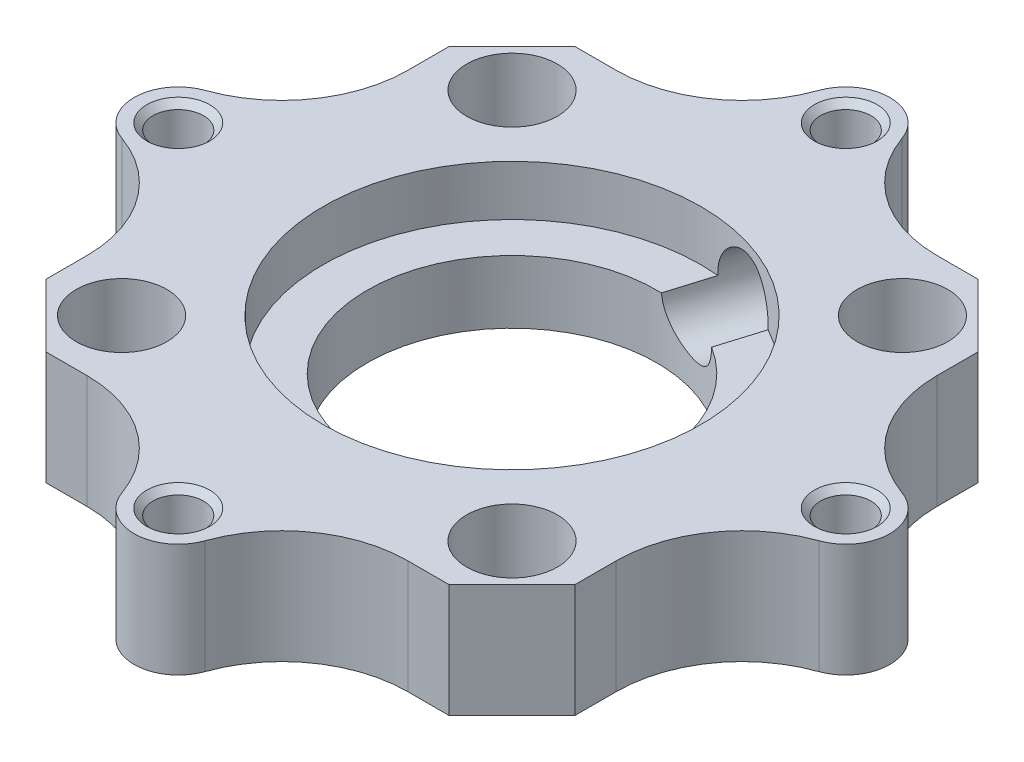
SolidWorks part; units mm, degrees
ref_plane "Front Plane" through (0, 0, 0) normal (0, 0, 1) x (1, 0, 0)
ref_plane "Top Plane" through (0, 0, 0) normal (0, 1, 0) x (1, 0, 0)
ref_plane "Right Plane" through (0, 0, 0) normal (1, 0, 0) x (0, 0, -1)
sketch "Sketch1" plane through (0, 0, 0) normal (0, 1, 0) x (1, 0, 0)
  line L1 (-30, -30) -> (30, -30)
  line L2 (-30, -30) -> (-30, 30)
  line L3 (-30, 30) -> (30, 30)
  line L4 (30, -30) -> (30, 30)
  line L5 (-30, -30) -> (30, 30) construction
  line L6 (-30, 30) -> (30, -30) construction
  circle A0 centre (0, 0) radius 11.5
  point P0 (0, 0)
  dimension "D2" = 23
  dimension "D1" = 60
extrude "Boss-Extrude1" add sketch "Sketch1" along normal blind 5
sketch "Sketch2" plane through (0, 5, 0) normal (0, 1, 0) x (1, 0, 0)
  line L1 (30, -30) -> (-30, -30)
  line L2 (30, -30) -> (30, 30)
  line L3 (30, 30) -> (-30, 30)
  line L4 (-30, -30) -> (-30, 30)
  line L5 (30, -30) -> (-30, 30) construction
  line L6 (30, 30) -> (-30, -30) construction
  circle A0 centre (0, 0) radius 30
  line M1 (30, -30) -> (30, 30)
  line M2 (30, 30) -> (-30, 30)
  line M3 (-30, 30) -> (-30, -30)
  line M4 (-30, -30) -> (30, -30)
extrude "Cut-Extrude1" cut sketch "Sketch2" against normal blind 10 contours A0 L3 M3 | A0 L2 M2 | A0 L1 M1 | A0 L4 M4
sketch "Sketch3" plane through (0, 5, 0) normal (0, 1, 0) x (1, 0, 0)
  line L0 (-12.9544, 12.9544) -> (0, 0) construction
  line L1 (-11.9, -15.5) -> (11.9, -15.5) construction
  line L2 (-15.5, -11.9) -> (-15.5, 11.9) construction
  line L3 (-11.9, 15.5) -> (11.9, 15.5) construction
  line L4 (15.5, -11.9) -> (15.5, 11.9) construction
  line L5 (-12.9544, -12.9544) -> (12.9544, 12.9544) construction
  line L6 (0, 0) -> (12.9544, -12.9544) construction
  line L7 (11.9, 15.5) -> (15.5, 15.5) construction
  line L8 (12.9544, 12.9544) -> (15.5, 15.5) construction
  line L9 (15.5, 11.9) -> (15.5, 15.5) construction
  line L10 (-15.5, 15.5) -> (-11.9, 15.5) construction
  line L11 (-15.5, 15.5) -> (-12.9544, 12.9544) construction
  line L12 (-15.5, 11.9) -> (-15.5, 15.5) construction
  line L13 (-15.5, -15.5) -> (-11.9, -15.5) construction
  line L14 (-15.5, -15.5) -> (-12.9544, -12.9544) construction
  line L15 (-15.5, -15.5) -> (-15.5, -11.9) construction
  line L16 (11.9, -15.5) -> (15.5, -15.5) construction
  line L17 (12.9544, -12.9544) -> (15.5, -15.5) construction
  line L18 (15.5, -15.5) -> (15.5, -11.9) construction
  circle A0 centre (-15.5, 15.5) radius 3.6
  circle A1 centre (15.5, 15.5) radius 3.6
  circle A2 centre (15.5, -15.5) radius 3.6
  circle A3 centre (-15.5, -15.5) radius 3.6
  arc A4 (-15.5, 15.5) -> (-17.828, 12.754) centre (0, 0) ccw construction
  arc A5 (12.754, 17.828) -> (-12.754, 17.828) centre (0, 0) ccw construction
  arc A6 (-17.828, 12.754) -> (-17.828, -12.754) centre (0, 0) ccw construction
  arc A7 (-17.828, -12.754) -> (-15.5, -15.5) centre (0, 0) ccw construction
  arc A8 (-12.754, -17.828) -> (12.754, -17.828) centre (0, 0) ccw construction
  arc A9 (15.5, -15.5) -> (17.828, -12.754) centre (0, 0) ccw construction
  arc A10 (17.828, -12.754) -> (17.828, 12.754) centre (0, 0) ccw construction
  arc A11 (17.828, 12.754) -> (15.5, 15.5) centre (0, 0) ccw construction
  arc A12 (15.5, 15.5) -> (12.754, 17.828) centre (0, 0) ccw construction
  arc A13 (-12.754, 17.828) -> (-15.5, 15.5) centre (0, 0) ccw construction
  arc A14 (-15.5, -15.5) -> (-12.754, -17.828) centre (0, 0) ccw construction
  arc A15 (12.754, -17.828) -> (15.5, -15.5) centre (0, 0) ccw construction
  point P0 (0, 0)
  point P17 (0, 0)
  dimension "D2" = 7.2
  dimension "D1" = 31
  dimension "D3" = 4
extrude "Cut-Extrude2" cut sketch "Sketch3" against normal blind 3
sketch "Sketch4" plane through (0, 2, 0) normal (0, 1, 0) x (1, 0, 0)
  circle A0 centre (-15.5, 15.5) radius 1.6
  circle A1 centre (15.5, 15.5) radius 1.6
  circle A2 centre (15.5, -15.5) radius 1.6
  circle A3 centre (-15.5, -15.5) radius 1.6
  point P12 (0, 0)
  dimension "D1" = 3.2
  dimension "D2" = 4
extrude "Cut-Extrude3" cut sketch "Sketch4" against normal blind 3
sketch "Sketch5" plane through (0, 5, 0) normal (0, 1, 0) x (1, 0, 0)
  line L0 (0, 30) -> (0, -30) construction
  line L1 (-23, 0) -> (23, 0) construction
  line L2 (-30, 0) -> (-23, 0) construction
  arc A0 (-30, 0) -> (-23, 0) centre (-26.5, 0) ccw construction
  arc A1 (-23, 0) -> (-30, 0) centre (-26.5, 0) ccw construction
  circle A2 centre (-26.5, 0) radius 2
  circle A3 centre (0, 26.5) radius 2
  circle A4 centre (26.5, 0) radius 2
  circle A5 centre (0, -26.5) radius 2
  point P5 (0, 0)
  point P6 (0, 0)
  point P19 (0, 0)
  dimension "D2" = 7
  dimension "D3" = 4
  dimension "D1" = 60
  dimension "D4" = 4
extrude "Cut-Extrude4" cut sketch "Sketch5" against normal through all
sketch "Sketch6" plane through (0, 5, 0) normal (0, 1, 0) x (1, 0, 0)
  line L0 (3.5, 21) -> (21, 21)
  line L1 (-26.5, 3.5) -> (-21, 3.5)
  line L2 (-26.5, -3.5) -> (-21, -3.5)
  line L3 (21, 3.5) -> (21, 21)
  line L4 (3.5, 26.5) -> (3.5, 21)
  line L5 (-3.5, 26.5) -> (-3.5, 21)
  line L6 (3.5, -21) -> (21, -21)
  line L7 (-21, -21) -> (-3.5, -21)
  line L8 (-21, -21) -> (-21, -3.5)
  line L9 (-21, 21) -> (-3.5, 21)
  line L10 (21, -21) -> (21, -3.5)
  line L11 (-21, 3.5) -> (-21, 21)
  line L15 (-3.5, -21) -> (-3.5, -26.5)
  line L17 (3.5, -21) -> (3.5, -26.5)
  line L18 (21, -3.5) -> (26.5, -3.5)
  line L20 (21, 3.5) -> (26.5, 3.5)
  arc A0 (-26.5, 3.5) -> (-26.5, -3.5) centre (-26.5, 0) ccw
  arc A1 (26.5, -3.5) -> (26.5, 3.5) centre (26.5, 0) ccw
  arc A2 (3.5, 26.5) -> (-3.5, 26.5) centre (0, 26.5) ccw
  arc A3 (-3.5, -26.5) -> (3.5, -26.5) centre (0, -26.5) ccw
  circle A4 centre (0, 0) radius 30
  point P4 (0, 0)
  point P9 (0, 0)
  point P18 (0, 0)
  circle M23 centre (0, 0) radius 30
  dimension "D1" = 3.5
  dimension "D2" = 3.5
  dimension "D3" = 42
extrude "Cut-Extrude5" cut sketch "Sketch6" against normal through all contours A2 A0 L1 L11 L9 L5 M23 | A2 L4 L0 L3 L20 A1 M23 | A3 L15 L7 L8 L2 A0 M23 | A3 A1 L18 L10 L6 L17 M23
chamfer "Chamfer1" distance 5 angle 45 4 edges at (-21, 2.5, -21) (-21, 2.5, 21) (21, 2.5, 21) (21, 2.5, -21)
fillet "Fillet1" radius 10 8 edges at (3.5, 2.5, -21) (-3.5, 2.5, -21) (-21, 2.5, -3.5) (-21, 2.5, 3.5) (-3.5, 2.5, 21) (3.5, 2.5, 21) (21, 2.5, 3.5) (21, 2.5, -3.5)
sketch "Sketch7" plane through (0, 5, 0) normal (0, 1, 0) x (1, 0, 0)
  line L12 (-21, -12.7279) -> (-21, -16)
  line L13 (-21, -16) -> (-16, -21)
  line L14 (-16, -21) -> (-12.7279, -21)
  line L15 (12.7279, -21) -> (16, -21)
  line L16 (16, -21) -> (21, -16)
  line L17 (21, -16) -> (21, -12.7279)
  line L18 (21, 12.7279) -> (21, 16)
  line L19 (21, 16) -> (16, 21)
  line L20 (16, 21) -> (12.7279, 21)
  line L21 (-12.7279, 21) -> (-16, 21)
  line L22 (-16, 21) -> (-21, 16)
  line L23 (-21, 16) -> (-21, 12.7279)
  line L24 (-21, -12.7279) -> (-21, -16)
  line L25 (-21, -16) -> (-16, -21)
  line L26 (-16, -21) -> (-12.7279, -21)
  line L27 (12.7279, -21) -> (16, -21)
  line L28 (16, -21) -> (21, -16)
  line L29 (21, -16) -> (21, -12.7279)
  line L30 (21, 12.7279) -> (21, 16)
  line L31 (21, 16) -> (16, 21)
  line L32 (16, 21) -> (12.7279, 21)
  line L33 (-12.7279, 21) -> (-16, 21)
  line L34 (-16, 21) -> (-21, 16)
  line L35 (-21, 16) -> (-21, 12.7279)
  circle A0 centre (-26.5, 0) radius 2
  circle A1 centre (0, 26.5) radius 2
  circle A2 centre (26.5, 0) radius 2
  circle A3 centre (0, -26.5) radius 2
  circle A4 centre (-15.5, 15.5) radius 3.6
  circle A5 centre (15.5, 15.5) radius 3.6
  circle A6 centre (15.5, -15.5) radius 3.6
  circle A7 centre (-15.5, -15.5) radius 3.6
  circle A8 centre (0, 0) radius 11.5
  arc A12 (-3.2998, -27.6667) -> (-12.7279, -21) centre (-12.7279, -31) ccw
  arc A13 (-3.2998, -27.6667) -> (3.2998, -27.6667) centre (0, -26.5) ccw
  arc A14 (12.7279, -21) -> (3.2998, -27.6667) centre (12.7279, -31) ccw
  arc A15 (27.6667, -3.2998) -> (21, -12.7279) centre (31, -12.7279) ccw
  arc A16 (27.6667, -3.2998) -> (27.6667, 3.2998) centre (26.5, 0) ccw
  arc A17 (21, 12.7279) -> (27.6667, 3.2998) centre (31, 12.7279) ccw
  arc A18 (3.2998, 27.6667) -> (12.7279, 21) centre (12.7279, 31) ccw
  arc A19 (3.2998, 27.6667) -> (-3.2998, 27.6667) centre (0, 26.5) ccw
  arc A20 (-12.7279, 21) -> (-3.2998, 27.6667) centre (-12.7279, 31) ccw
  arc A21 (-27.6667, 3.2998) -> (-21, 12.7279) centre (-31, 12.7279) ccw
  arc A22 (-27.6667, 3.2998) -> (-27.6667, -3.2998) centre (-26.5, 0) ccw
  arc A23 (-21, -12.7279) -> (-27.6667, -3.2998) centre (-31, -12.7279) ccw
  arc A24 (-3.2998, -27.6667) -> (-12.7279, -21) centre (-12.7279, -31) ccw
  arc A25 (-3.2998, -27.6667) -> (3.2998, -27.6667) centre (0, -26.5) ccw
  arc A26 (12.7279, -21) -> (3.2998, -27.6667) centre (12.7279, -31) ccw
  arc A27 (27.6667, -3.2998) -> (21, -12.7279) centre (31, -12.7279) ccw
  arc A28 (27.6667, -3.2998) -> (27.6667, 3.2998) centre (26.5, 0) ccw
  arc A29 (21, 12.7279) -> (27.6667, 3.2998) centre (31, 12.7279) ccw
  arc A30 (3.2998, 27.6667) -> (12.7279, 21) centre (12.7279, 31) ccw
  arc A31 (3.2998, 27.6667) -> (-3.2998, 27.6667) centre (0, 26.5) ccw
  arc A32 (-12.7279, 21) -> (-3.2998, 27.6667) centre (-12.7279, 31) ccw
  arc A33 (-27.6667, 3.2998) -> (-21, 12.7279) centre (-31, 12.7279) ccw
  arc A34 (-27.6667, 3.2998) -> (-27.6667, -3.2998) centre (-26.5, 0) ccw
  arc A35 (-21, -12.7279) -> (-27.6667, -3.2998) centre (-31, -12.7279) ccw
  point P39 (0, 0)
  point P54 (0, 0)
  dimension "D1" = 0
  dimension "D2" = 4
  dimension "D3" = 4
extrude "Boss-Extrude2" add sketch "Sketch7" along normal blind 4
sketch "Sketch8" plane through (0, 9, 0) normal (0, 1, 0) x (1, 0, 0)
  circle A0 centre (0, 0) radius 15
  dimension "D1" = 30
extrude "Cut-Extrude6" cut sketch "Sketch8" against normal blind 4
sketch "Sketch9" plane through (0, 9, 0) normal (0, 1, 0) x (1, 0, 0)
  line L0 (0, 0) -> (30, 0) construction
  line L1 (0, 0) -> (0, 30) construction
  line L2 (0, 30) -> (6.9544, 22.835) construction
  line L3 (6.9544, 22.835) -> (0, 0) construction
  arc A0 (27.6667, -3.2998) -> (27.6667, 3.2998) centre (26.5, 0) ccw construction
  arc A1 (3.2998, 27.6667) -> (-3.2998, 27.6667) centre (0, 26.5) ccw construction
  arc A2 (3.2998, 27.6667) -> (12.7279, 21) centre (12.7279, 31) ccw construction
ref_plane "Plane1" through (6.8067, 0, -22.3499) normal (0.2913, 0, -0.9566) x (-0.9566, 0, -0.2913)
sketch "Sketch10" plane through (6.8067, 0, -22.3499) normal (0.2913, 0, -0.9566) x (-0.9566, 0, -0.2913)
  line L0 (0, 8.9079) -> (0, 0) construction
  circle A0 centre (0, 5.2353) radius 3
  dimension "D1" = 6
extrude "Cut-Extrude7" cut sketch "Sketch10" against normal blind 16 and the other way blind 10
chamfer "Chamfer2" distance 0.5 angle 45 4 edges at (-26.5, 9, 2) (0, 9, -24.5) (26.5, 9, 2) (0, 9, 28.5)
